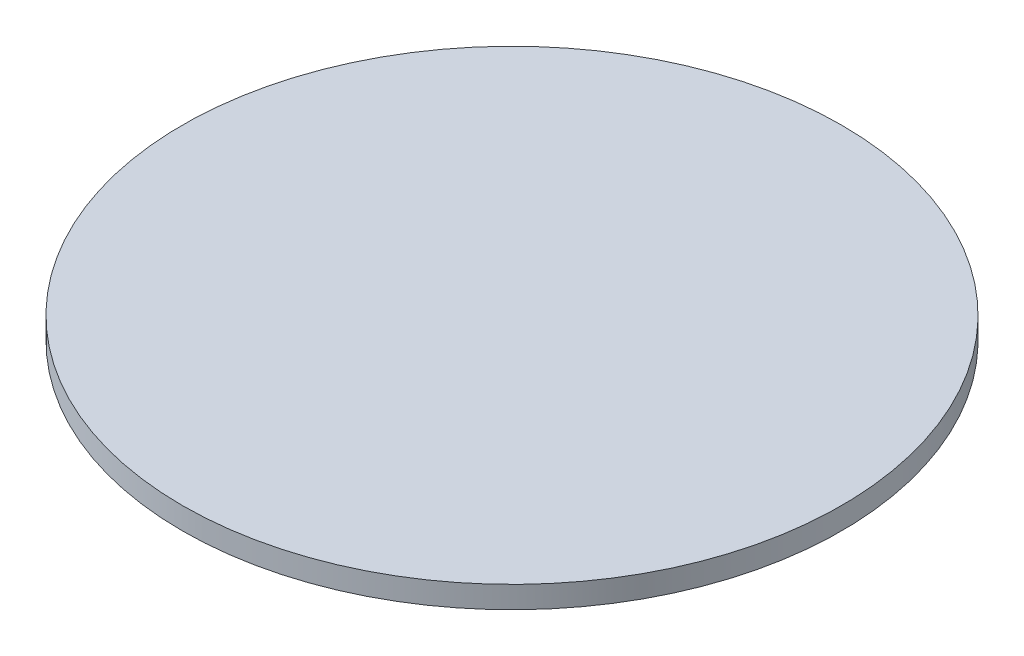
SolidWorks part; units mm, degrees
ref_plane "Front Plane" through (0, 0, 0) normal (0, 0, 1) x (1, 0, 0)
ref_plane "Top Plane" through (0, 0, 0) normal (0, 1, 0) x (1, 0, 0)
ref_plane "Right Plane" through (0, 0, 0) normal (1, 0, 0) x (0, 0, -1)
sketch "Sketch1" plane through (0, 0, 0) normal (0, 1, 0) x (1, 0, 0)
  circle A0 centre (0, 0) radius 38.1
  dimension "D1" = 76.2
extrude "Boss-Extrude1" add sketch "Sketch1" along normal blind 2.54
